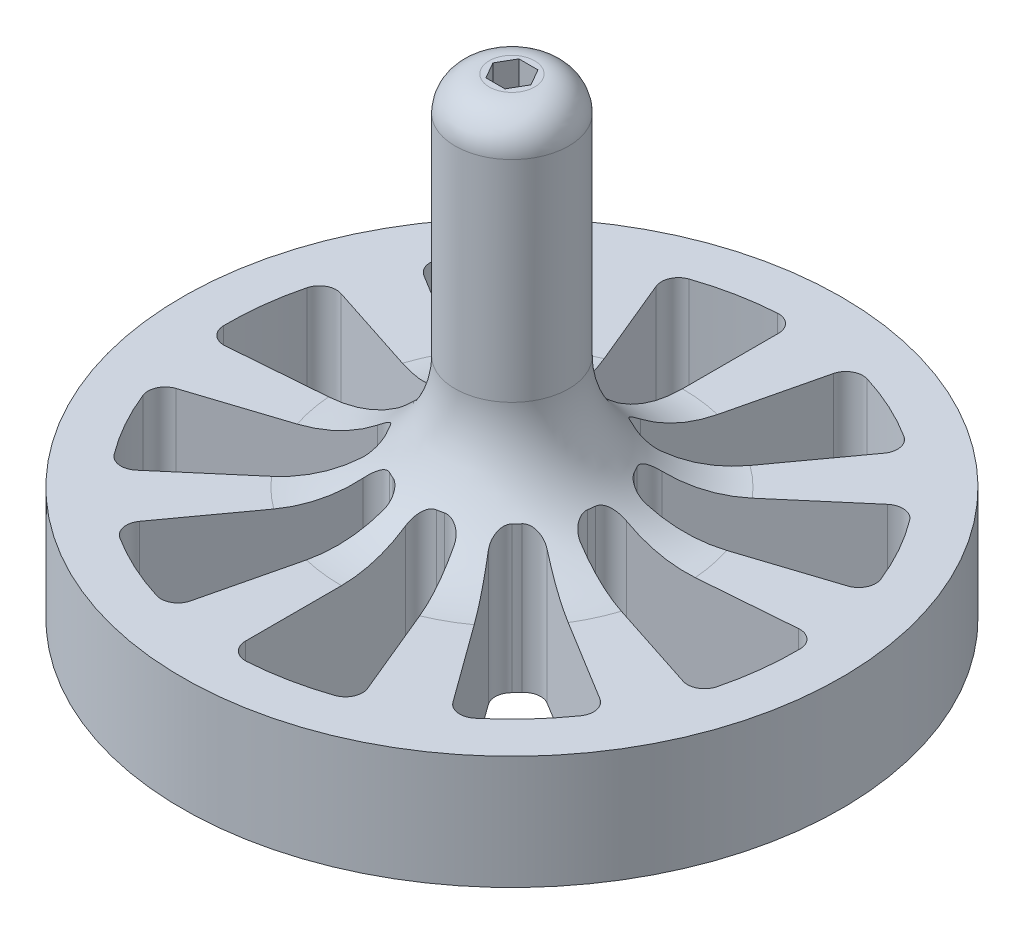
SolidWorks part; units mm, degrees
ref_plane "Płaszczyzna przednia" through (0, 0, 0) normal (0, 0, 1) x (1, 0, 0)
ref_plane "Płaszczyzna górna" through (0, 0, 0) normal (0, 1, 0) x (1, 0, 0)
ref_plane "Płaszczyzna prawa" through (0, 0, 0) normal (1, 0, 0) x (0, 0, -1)
sketch "Szkic1" plane through (0, 0, 0) normal (0, 0, 1) x (1, 0, 0)
  line L0 (0, 0) -> (0, 72.5) construction
  line L1 (-38.6719, 72.5) -> (38.6719, 72.5) construction
  line L2 (29, 10) -> (15, 10)
  line L3 (0, 0) -> (29, 0)
  line L6 (29, 0) -> (29, 10)
  line L7 (5, 20) -> (5, 41.5)
  line L8 (-55.3126, 21.5) -> (55.3126, 21.5) construction
  line L9 (5, 41.5) -> (0, 41.5)
  line L10 (0, 41.5) -> (0, 0)
  arc A0 (15, 10) -> (5, 20) centre (15, 20) cw
  point P2 (0, 21.5)
  dimension "D7" = 10
  dimension "D1" = 72.5
  dimension "D2" = 29
  dimension "D3" = 10
  dimension "D4" = 51
  dimension "D5" = 20
  dimension "D6" = 5
revolve "Obrót1" add sketch "Szkic1" angle 360 about L0
sketch "Szkic2" plane through (0, 0, 0) normal (0, -1, 0) x (1, 0, 0)
  line L1 (1.6743, 0) -> (0.8372, 1.45)
  line L2 (0.8372, 1.45) -> (-0.8372, 1.45)
  line L3 (-0.8372, 1.45) -> (-1.6743, 0)
  line L4 (-1.6743, 0) -> (-0.8372, -1.45)
  line L5 (-0.8372, -1.45) -> (0.8372, -1.45)
  line L6 (0.8372, -1.45) -> (1.6743, 0)
  circle A0 centre (0, 0) radius 1.45 construction
  dimension "D1" = 2.9
extrude "Wytnij-wyciągnięcie1" cut sketch "Szkic2" against normal up to surface (41.5 mm away) up to face at (0, 41.5, -5)
fillet "Zaokrąglenie1" radius 3 1 edges at (0, 41.5, -5)
sketch "Szkic4" plane through (0, 0, 0) normal (0, -1, 0) x (1, 0, 0)
  line L0 (0, 29) -> (0, 0) construction
  line L1 (0, 0) -> (11.0978, 26.7925) construction
  line L2 (0, 23.4521) -> (0, 9.3808)
  line L3 (3.5899, 8.6668) -> (8.9747, 21.6669)
  circle A0 centre (0, 0) radius 29 construction
  arc A1 (1.2632, 7.8996) -> (1.8561, 7.7817) centre (0, 0) cw
  arc A2 (1.5957, 24.949) -> (8.0733, 23.6606) centre (0, 0) cw
  arc A3 (8.0733, 23.6606) -> (8.9747, 21.6669) centre (7.5889, 22.2409) cw
  arc A4 (1.8561, 7.7817) -> (3.5899, 8.6668) centre (2.2041, 9.2408) ccw
  arc A5 (1.2632, 7.8996) -> (0, 9.3808) centre (1.5, 9.3808) cw
  arc A6 (1.5957, 24.949) -> (0, 23.4521) centre (1.5, 23.4521) ccw
  point P12 (9.5671, 23.097)
  point P15 (3.0615, 7.391)
  point P18 (0, 8)
  point P21 (0, 25)
  dimension "D2" = 25
  dimension "D3" = 8
  dimension "D4" = 1.5
  dimension "D1" = 22.5
extrude "Wytnij-wyciągnięcie2" cut sketch "Szkic4" against normal through all
pattern_circular "Szyk kołowy1" count 10 over 360 about axis through (0, 0, 0) along (0, 1, 0) of "Wytnij-wyciągnięcie2"
